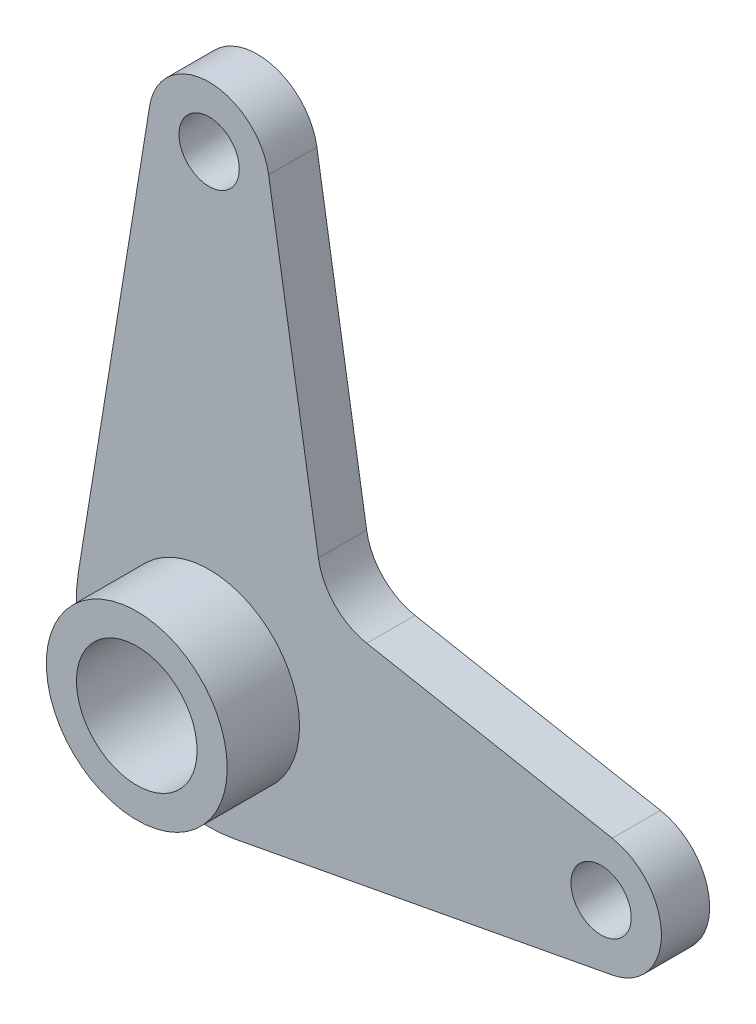
SolidWorks part; units mm, degrees
ref_plane "Front Plane" through (0, 0, 0) normal (0, 0, 1) x (1, 0, 0)
ref_plane "Top Plane" through (0, 0, 0) normal (0, 1, 0) x (1, 0, 0)
ref_plane "Right Plane" through (0, 0, 0) normal (1, 0, 0) x (0, 0, -1)
sketch "Sketch1" plane through (0, 0, 0) normal (0, 0, 1) x (1, 0, 0)
  line L0 (-9.8712, 76.6) -> (-21.7166, 3.52)
  line L1 (9.8712, 76.6) -> (18.1212, 25.7015)
  line L2 (4.0615, -21.6218) -> (66.8462, -9.8281)
  line L3 (26.1462, 17.4734) -> (66.8462, 9.8281)
  arc A0 (-21.7166, 3.52) -> (4.0615, -21.6218) centre (0, 0) ccw
  circle A1 centre (0, 75) radius 5
  arc A2 (9.8712, 76.6) -> (-9.8712, 76.6) centre (0, 75) ccw
  arc A3 (66.8462, -9.8281) -> (66.8462, 9.8281) centre (65, 0) ccw
  circle A4 centre (65, 0) radius 5
  arc A5 (26.1462, 17.4734) -> (18.1212, 25.7015) centre (27.9924, 27.3015) cw
  dimension "D1" = 44
  dimension "D2" = 20
  dimension "D3" = 10
  dimension "D6" = 10
  dimension "D4" = 75
  dimension "D5" = 65
extrude "Boss-Extrude1" add sketch "Sketch1" along normal blind 8
sketch "Sketch2" plane through (0, 0, 8) normal (0, 0, 1) x (1, 0, 0)
  circle A0 centre (0, 0) radius 15
  dimension "D1" = 30
extrude "Boss-Extrude2" add sketch "Sketch2" along normal blind 12
sketch "Sketch3" plane through (0, 0, 20) normal (0, 0, 1) x (1, 0, 0)
  circle A0 centre (0, 0) radius 10
  dimension "D1" = 20
extrude "Cut-Extrude1" cut sketch "Sketch3" against normal through all
